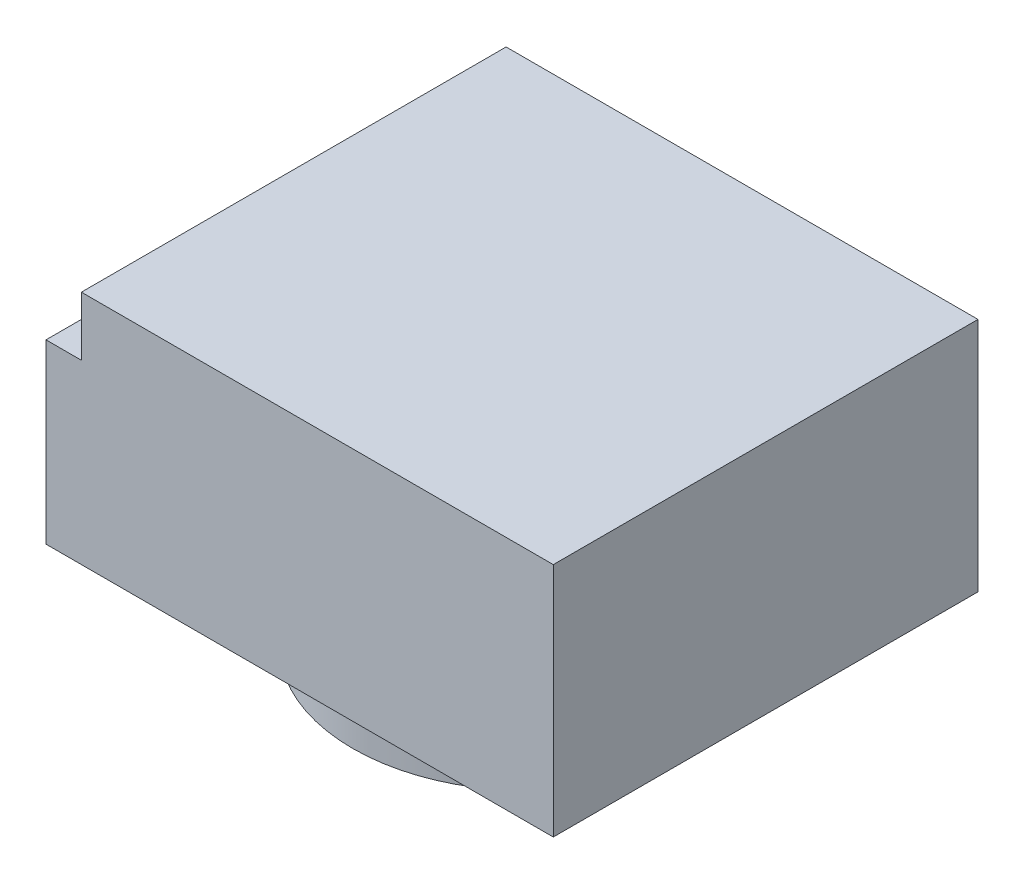
SolidWorks part; units mm, degrees
ref_plane "Alzado" through (0, 0, 0) normal (0, 0, 1) x (1, 0, 0)
ref_plane "Planta" through (0, 0, 0) normal (0, 1, 0) x (1, 0, 0)
ref_plane "Vista lateral" through (0, 0, 0) normal (1, 0, 0) x (0, 0, -1)
sketch "Croquis1" plane through (0, 0, 0) normal (0, 1, 0) x (1, 0, 0)
  line L1 (-20, -18) -> (20, -18)
  line L2 (-20, -18) -> (-20, 18)
  line L3 (-20, 18) -> (20, 18)
  line L4 (20, -18) -> (20, 18)
  line L5 (-20, -18) -> (20, 18) construction
  line L6 (-20, 18) -> (20, -18) construction
  point P0 (0, 0)
  dimension "D1" = 36
  dimension "D2" = 40
extrude "Saliente-Extruir1" add sketch "Croquis1" along normal blind 20
sketch "Croquis2" plane through (0, 0, 0) normal (1, 0, 0) x (0, 0, -1)
  line L0 (0, 0) -> (0, -265.4363) construction
  line L1 (0, 0) -> (-15, 1.0227)
  line L3 (-15, 1.0227) -> (-15, -5)
  line L4 (-15, -5) -> (0, -5)
  line L14 (0, 0) -> (0, -5)
  dimension "D2" = 30
  dimension "D3" = 5
sketch "Croquis3" plane through (0, 0, 0) normal (0, 0, 1) x (1, 0, 0)
  line L0 (-20, 0) -> (-23, 0)
  line L1 (-23, 0) -> (-23, 15)
  line L2 (-23, 15) -> (-20, 15)
  line L4 (-20, 15) -> (-20, 0)
  line L6 (-20, 20) -> (20, 20) construction
  dimension "D1" = 3
  dimension "D2" = 5
revolve "Revolución1" add sketch "Croquis2" angle 360 about L0
extrude "Saliente-Extruir2" add sketch "Croquis3" along normal up to vertex (18 mm away) and the other way up to vertex (18 mm away)
